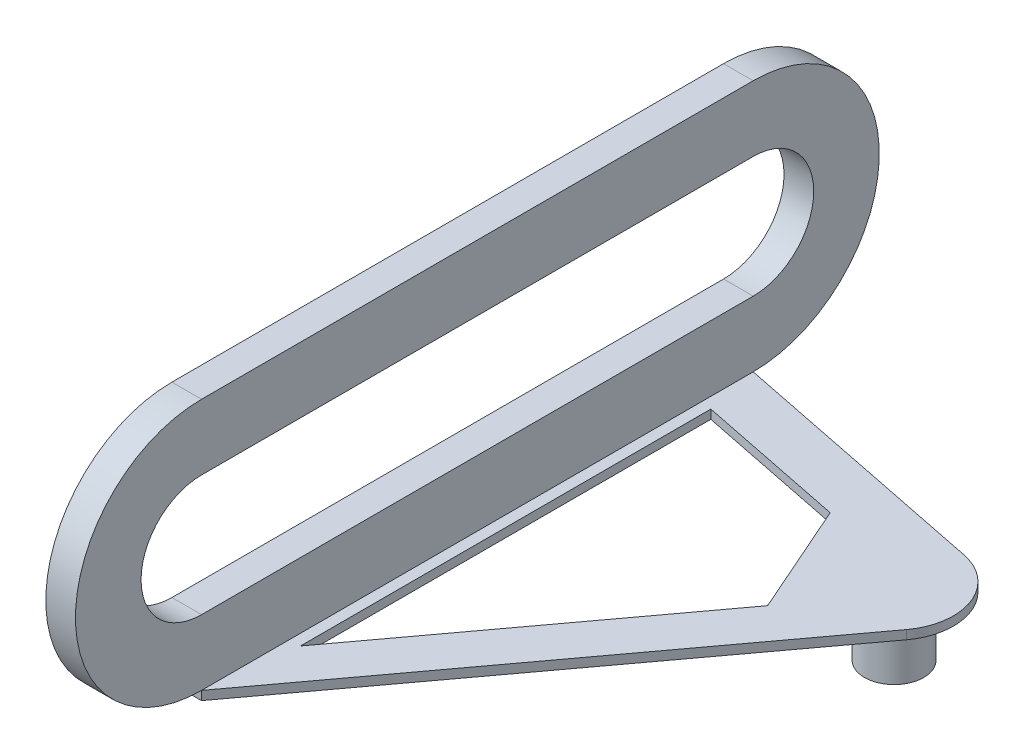
SolidWorks part; units mm, degrees
material "1060 Alloy"
ref_plane "Front Plane" through (0, 0, 0) normal (0, 0, 1) x (1, 0, 0)
ref_plane "Top Plane" through (0, 0, 0) normal (0, 1, 0) x (1, 0, 0)
ref_plane "Right Plane" through (0, 0, 0) normal (1, 0, 0) x (0, 0, -1)
ref_plane "Plane1" through (10, 0, 0) normal (1, 0, 0) x (0, 0, -1)
sketch "Sketch1" plane through (10, 0, 0) normal (1, 0, 0) x (0, 0, -1)
  line L0 (0, 42.5) -> (-186, 42.5)
  line L1 (-186, -42.5) -> (0, -42.5)
  arc A0 (0, -42.5) -> (0, 42.5) centre (0, 0) ccw
  arc A1 (-186, 42.5) -> (-186, -42.5) centre (-186, 0) ccw
extrude "Boss-Extrude1" add sketch "Sketch1" against normal blind 10
sketch "Sketch2" plane through (0, -42.5, 0) normal (0, -1, 0) x (1, 0, 0)
  line L0 (98.9444, 17.8928) -> (10, 0)
  line L1 (10, 0) -> (0, 0)
  line L2 (0, 0) -> (0, 186)
  line L3 (0, 186) -> (10, 186)
  line L4 (10, 186) -> (111.0774, 49.3961)
  arc A0 (111.0774, 49.3961) -> (98.9444, 17.8928) centre (95, 37.5) cw
extrude "Boss-Extrude2" add sketch "Sketch2" along normal blind 3
sketch "Sketch3" plane through (0, -45.5, 0) normal (0, -1, 0) x (1, 0, 0)
  circle A0 centre (95, 37.5) radius 10
extrude "Boss-Extrude3" add sketch "Sketch3" along normal blind 20
sketch "Sketch4" plane through (10, 0, 0) normal (1, 0, 0) x (0, 0, -1)
  line L0 (-186, -20.39) -> (0, -20.39)
  line L1 (0, 20.39) -> (-186, 20.39)
  arc A0 (-186, 20.39) -> (-186, -20.39) centre (-186, 0) ccw
  arc A1 (0, -20.39) -> (0, 20.39) centre (0, 0) ccw
extrude "Cut-Extrude1" cut sketch "Sketch4" against normal through all
sketch "Sketch5" plane through (0, -45.5, 0) normal (0, -1, 0) x (1, 0, 0)
  line L0 (13.7159, 156.3592) -> (13.7159, 18.016)
  line L1 (13.7159, 18.016) -> (64.1029, 28.1523)
  line L2 (64.1029, 28.1523) -> (80.693, 65.8412)
  line L3 (80.693, 65.8412) -> (13.7159, 156.3592)
extrude "Cut-Extrude2" cut sketch "Sketch5" against normal through all
